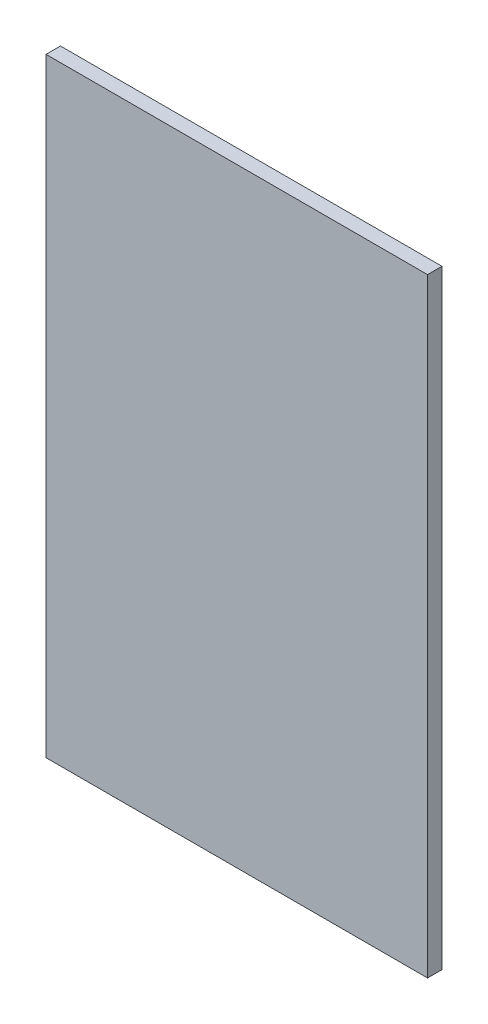
SolidWorks part; units mm, degrees
ref_plane "Front Plane" through (0, 0, 0) normal (0, 0, 1) x (1, 0, 0)
ref_plane "Top Plane" through (0, 0, 0) normal (0, 1, 0) x (1, 0, 0)
ref_plane "Right Plane" through (0, 0, 0) normal (1, 0, 0) x (0, 0, -1)
sketch "Sketch1" plane through (0, 0, 0) normal (0, 0, 1) x (1, 0, 0)
  line L1 (238, -380) -> (-238, -380)
  line L2 (238, -380) -> (238, 380)
  line L3 (238, 380) -> (-238, 380)
  line L4 (-238, -380) -> (-238, 380)
  line L5 (238, -380) -> (-238, 380) construction
  line L6 (238, 380) -> (-238, -380) construction
  point P0 (0, 0)
  dimension "D1" = 760
  dimension "D2" = 476
extrude "Boss-Extrude1" add sketch "Sketch1" along normal blind 18
equation "\"H_DSP\"=18"
equation "\"D1@Boss-Extrude1\"=\"H_DSP\""
